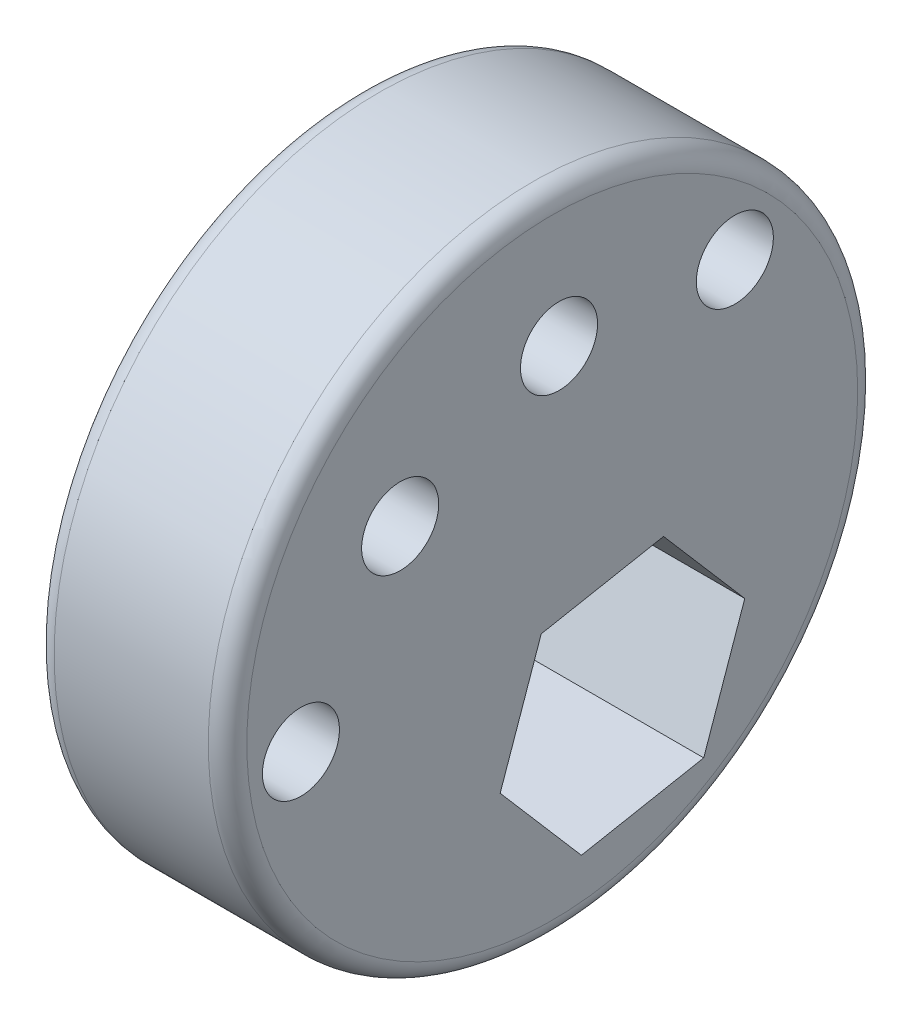
SolidWorks part; units mm, degrees
ref_plane "Ebene vorne" through (0, 0, 0) normal (0, 0, 1) x (1, 0, 0)
ref_plane "Ebene oben" through (0, 0, 0) normal (0, 1, 0) x (1, 0, 0)
ref_plane "Ebene rechts" through (0, 0, 0) normal (1, 0, 0) x (0, 0, -1)
sketch "Skizze1" plane through (0, 0, 0) normal (1, 0, 0) x (0, 0, -1)
  circle A0 centre (0, 0) radius 8.425
  dimension "D1" = 16.85
extrude "Aufsatz-Linear austragen1" add sketch "Skizze1" along normal blind 5
sketch "Skizze2" plane through (0, 0, 0) normal (1, 0, 0) x (0, 0, -1)
  line L0 (-0.2861, -1.3453) -> (2.8873, -0.7434)
  line L1 (2.8873, -0.7434) -> (4.9953, -3.1908)
  line L2 (4.9953, -3.1908) -> (3.9298, -6.24)
  line L3 (3.9298, -6.24) -> (0.7563, -6.8418)
  line L4 (0.7563, -6.8418) -> (-1.3516, -4.3945)
  line L5 (-1.3516, -4.3945) -> (-0.2861, -1.3453)
  line L6 (1.3136, -4.2303) -> (2.7978, -2.952) construction
  line L7 (1.6115, -2.6837) -> (1.9847, -4.6514) construction
  line L8 (1.1396, -3.5542) -> (2.9676, -4.193) construction
  line L9 (1.8269, -3.7916) -> (0.6708, -4.0109) construction
  line L10 (1.837, -3.8102) -> (1.069, -2.9186) construction
  line L11 (1.427, -4.9226) -> (1.8151, -3.8117) construction
  circle A0 centre (1.8218, -3.7926) radius 2.7973 construction
  circle A1 centre (1.8218, -3.7926) radius 8.8377 construction
  circle A2 centre (4.7372, 4.5504) radius 1
  circle A3 centre (0.1751, 4.8903) radius 1
  circle A4 centre (-3.9458, 2.9037) radius 1
  circle A5 centre (-6.5212, -0.8773) radius 1
  point P11 (-0.8189, -2.8699)
  point P15 (1.3006, -1.0443)
  point P16 (-0.2976, -5.6181)
  point P24 (4.7372, 4.5504)
  point P25 (0.1751, 4.8903)
  point P26 (-3.9458, 2.9037)
  point P27 (-6.5212, -0.8773)
  dimension "D7" = 2
  dimension "D8" = 2
  dimension "D9" = 2
  dimension "D10" = 2
  dimension "D1" = 120
  dimension "D2" = 120
  dimension "D3" = 120
  dimension "D4" = 3.23
  dimension "D5" = 3.23
  dimension "D6" = 0
extrude "Schnitt-Linear austragen1" cut sketch "Skizze2" along normal up to surface (5 mm away) up to face at (5, 0, -8.425)
fillet "Verrundung5" radius 0.5 1 edges at (5, 0, -8.425)
fillet "Verrundung6" radius 0.5 1 edges at (0, 0, -8.425)
sketch "Bezug" plane through (0, 0, 0) normal (-1, 0, 0) x (0, 0, 1)
  circle A0 centre (-1.8218, -3.7926) radius 3.23
